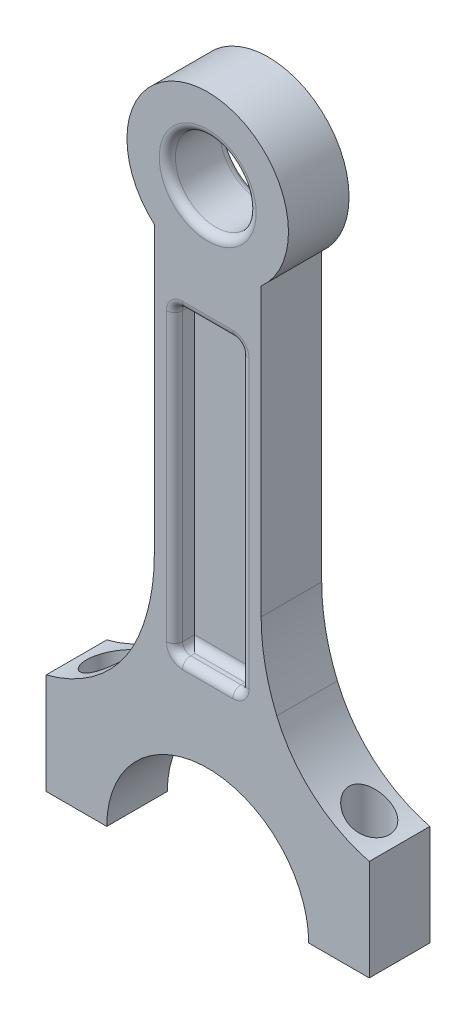
SolidWorks part; units mm, degrees
ref_plane "Front Plane" through (0, 0, 0) normal (0, 0, 1) x (1, 0, 0)
ref_plane "Top Plane" through (0, 0, 0) normal (0, 1, 0) x (1, 0, 0)
ref_plane "Right Plane" through (0, 0, 0) normal (1, 0, 0) x (0, 0, -1)
sketch "Sketch1" plane through (0, 0, 0) normal (0, 0, 1) x (1, 0, 0)
  line L4 (-13.2288, -15) -> (-13.2288, -85.9522)
  line L5 (13.2288, -15) -> (13.2288, -85.9522)
  line L7 (0, -120) -> (0, -150) construction
  line L8 (0, -120) -> (0, -125) construction
  line L9 (-40, -150) -> (-25, -150)
  line L11 (25, -150) -> (40, -150)
  arc A0 (13.2288, -15) -> (-13.2288, -15) centre (0, 0) ccw
  arc A1 (0, -125) -> (-25, -150) centre (0, -150) ccw
  arc A2 (0, -125) -> (25, -150) centre (0, -150) cw
  arc A3 (28.1017, -121.5343) -> (40, -150) centre (0, -150) cw
  arc A4 (-28.1017, -121.5343) -> (-40, -150) centre (0, -150) ccw
  arc A5 (-28.1017, -121.5343) -> (-13.2288, -85.9522) centre (-63.2288, -85.9522) ccw
  arc A6 (0, -110) -> (-40, -150) centre (0, -150) ccw construction
  arc A7 (0, -110) -> (40, -150) centre (0, -150) cw construction
  arc A8 (28.1017, -121.5343) -> (13.2288, -85.9522) centre (63.2288, -85.9522) cw
  dimension "D1" = 40
  dimension "D2" = 50
  dimension "D3" = 50
  dimension "D4" = 25
  dimension "D6" = 15
extrude "Boss-Extrude1" add sketch "Sketch1" along normal blind 7.5
sketch "Sketch2" plane through (0, 0, 7.5) normal (0, 0, 1) x (1, 0, 0)
  circle A0 centre (0, 0) radius 10
  dimension "D1" = 20
extrude "Cut-Extrude1" cut sketch "Sketch2" against normal through all
sketch "Sketch3" plane through (0, 0, 7.5) normal (0, 0, 1) x (1, 0, 0)
  line L0 (0, -10) -> (0, -125) construction
  line L1 (-8.2288, -104.9998) -> (-8.2288, -67.5) construction
  line L2 (-8.2288, -30.0002) -> (8.2288, -30.0002)
  line L3 (-8.2288, -30.0002) -> (-8.2288, -104.9998)
  line L4 (-8.2288, -104.9998) -> (8.2288, -104.9998)
  line L5 (8.2288, -30.0002) -> (8.2288, -104.9998)
  line L6 (-8.2288, -30.0002) -> (8.2288, -104.9998) construction
  line L7 (-8.2288, -104.9998) -> (8.2288, -30.0002) construction
  line L8 (-8.2288, -104.9998) -> (-8.2288, -54.9998) construction
  circle A0 centre (0, 0) radius 10 construction
  arc A1 (25, -150) -> (-25, -150) centre (0, -150) ccw construction
  point P7 (0, -67.5)
  point P15 (0, -104.9998)
extrude "Cut-Extrude2" cut sketch "Sketch3" against normal blind 5
fillet "Fillet2" radius 2 10 edges at (0, -30.0002, 7.5) (0, -104.9998, 7.5) (8.2288, -67.5, 7.5) (-8.2288, -67.5, 7.5) (0, -104.9998, 2.5) (0, -30.0002, 2.5) (-8.2288, -104.9998, 5) (8.2288, -104.9998, 5) (8.2288, -30.0002, 5) (-8.2288, -30.0002, 5)
mirror "Mirror1" about plane through (-63.2288, -85.9522, 0) normal (0, 0, 1) of bodies 103
fillet "Fillet3" radius 2 1 edges at (10, 0, 7.5)
sketch "Sketch7" plane through (0, 0, 7.5) normal (0, 0, 1) x (1, 0, 0)
  line L0 (-40, -150) -> (-40, -125)
  line L1 (0, -150) -> (0, -123.2784) construction
  line L4 (40, -150) -> (40, -125)
  arc A1 (-17.0966, -105.2349) -> (-40, -125) centre (-48.3504, -92.1711) cw
  arc A2 (-40, -150) -> (-28.1017, -121.5343) centre (0, -150) cw
  arc A4 (-28.1017, -121.5343) -> (-13.2288, -85.9522) centre (-63.2288, -85.9522) ccw construction
  arc A5 (-28.1017, -121.5343) -> (-17.0966, -105.2349) centre (-63.2288, -85.9522) ccw
  arc A6 (40, -150) -> (28.1017, -121.5343) centre (0, -150) ccw
  arc A7 (17.0966, -105.2349) -> (40, -125) centre (48.3504, -92.1711) ccw
  arc A8 (28.1017, -121.5343) -> (17.0966, -105.2349) centre (63.2288, -85.9522) cw
  dimension "D1" = 25
fillet "Fillet4" radius 2 1 edges at (10, 0, -7.5)
extrude "Boss-Extrude2" add sketch "Sketch7" against normal up to surface (15 mm away) up to face at (-12, 0, -7.5)
sketch "Sketch8" plane through (0, -150, 0) normal (0, -1, 0) x (-1, 0, 0)
  line L0 (25, 0) -> (40, 0) construction
  line L1 (25, -7.5) -> (25, 7.5) construction
  line L2 (40, -7.5) -> (40, 7.5) construction
  line L3 (0, 0) -> (0, -16.9306) construction
  circle A0 centre (32.5, 0) radius 5
  circle A1 centre (-32.5, 0) radius 5
  dimension "D1" = 10
extrude "Cut-Extrude3" cut sketch "Sketch8" against normal through all
